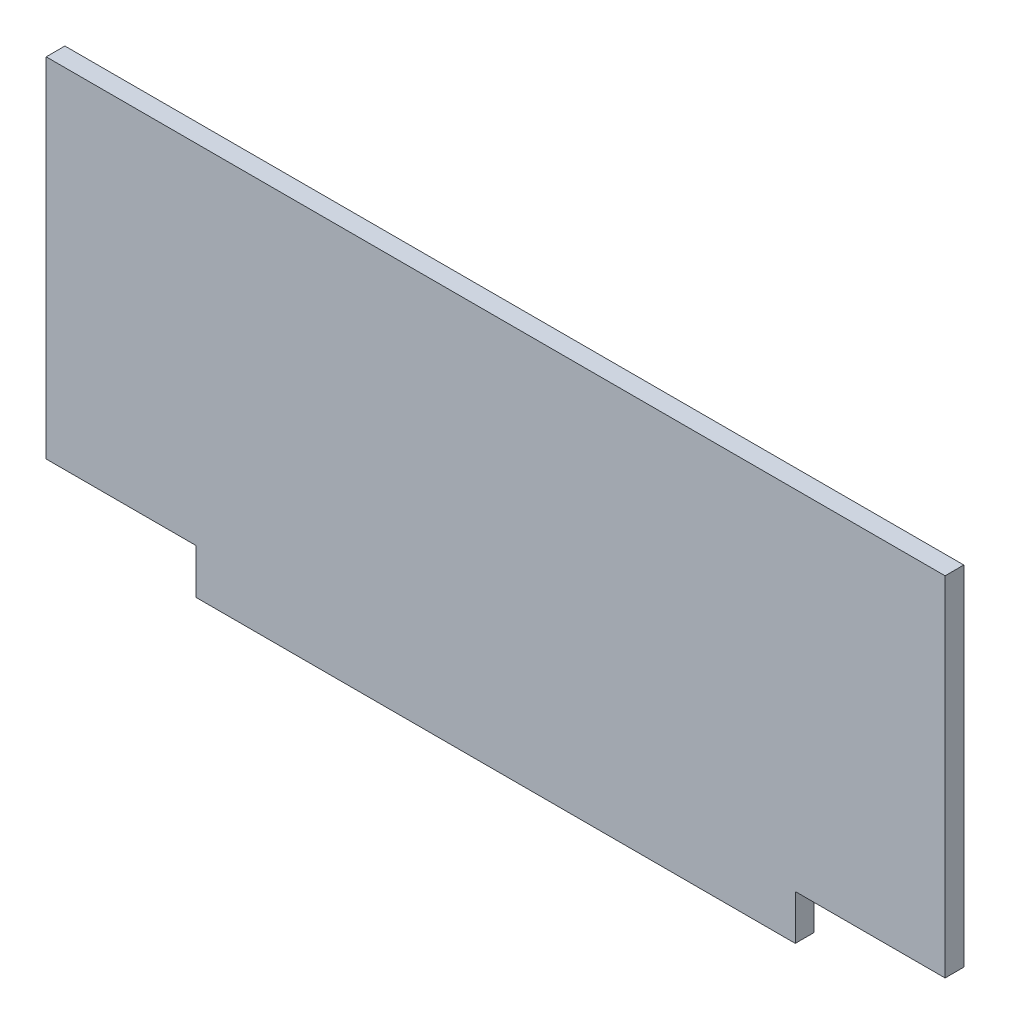
SolidWorks part; units mm, degrees
ref_plane "Plan de face" through (0, 0, 0) normal (0, 0, 1) x (1, 0, 0)
ref_plane "Plan de dessus" through (0, 0, 0) normal (0, 1, 0) x (1, 0, 0)
ref_plane "Plan de droite" through (0, 0, 0) normal (1, 0, 0) x (0, 0, -1)
sketch "Esquisse1" plane through (0, 0, 0) normal (0, 0, 1) x (1, 0, 0)
  line L1 (-290, 105) -> (190, 105)
  line L2 (-290, 105) -> (-290, -105)
  line L3 (-290, -105) -> (190, -105)
  line L4 (190, 105) -> (190, -105)
  dimension "D1" = 480
  dimension "D2" = 210
  dimension "D3" = 105
  dimension "D4" = 190
extrude "Boss.-Extru.1" add sketch "Esquisse1" along normal blind 10
sketch "Esquisse2" plane through (0, 0, 10) normal (0, 0, 1) x (1, 0, 0)
  line L1 (190, -105) -> (110, -105)
  line L2 (190, -105) -> (190, -81)
  line L3 (190, -81) -> (110, -81)
  line L4 (110, -105) -> (110, -81)
  line L5 (-290, -105) -> (-210, -105)
  line L6 (-290, -105) -> (-290, -81)
  line L7 (-290, -81) -> (-210, -81)
  line L8 (-210, -105) -> (-210, -81)
  dimension "D1" = 80
  dimension "D2" = 24
  dimension "D3" = 24
  dimension "D4" = 80
extrude "Enlèv. mat.-Extru.1" cut sketch "Esquisse2" against normal through all
